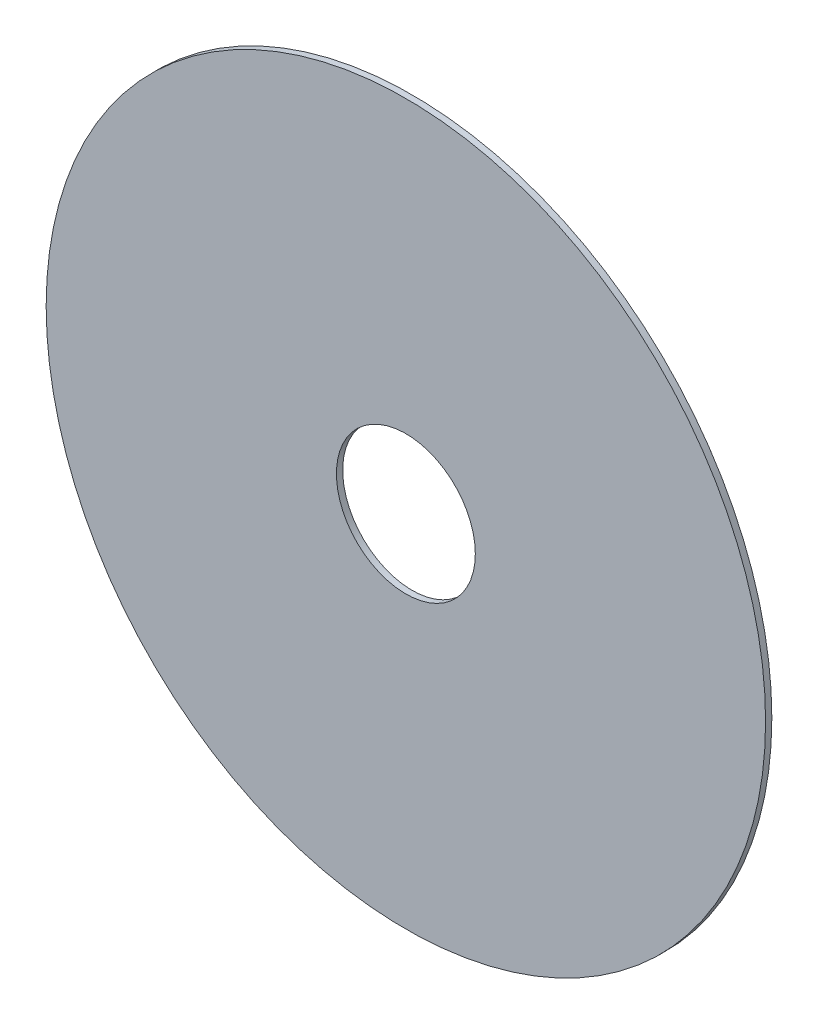
SolidWorks part; units mm, degrees
ref_plane "Płaszczyzna przednia" through (0, 0, 0) normal (0, 0, 1) x (1, 0, 0)
ref_plane "Płaszczyzna górna" through (0, 0, 0) normal (0, 1, 0) x (1, 0, 0)
ref_plane "Płaszczyzna prawa" through (0, 0, 0) normal (1, 0, 0) x (0, 0, -1)
sketch "Szkic2" plane through (0, 0, 0) normal (0, 0, 1) x (1, 0, 0)
  circle A0 centre (0, 0) radius 57.5
  circle A1 centre (0, 0) radius 11.1
  dimension "D1" = 115
  dimension "D2" = 22.2
extrude "Dodanie-wyciągnięcie1" add sketch "Szkic2" along normal blind 1
ref_point "Punkt1"
